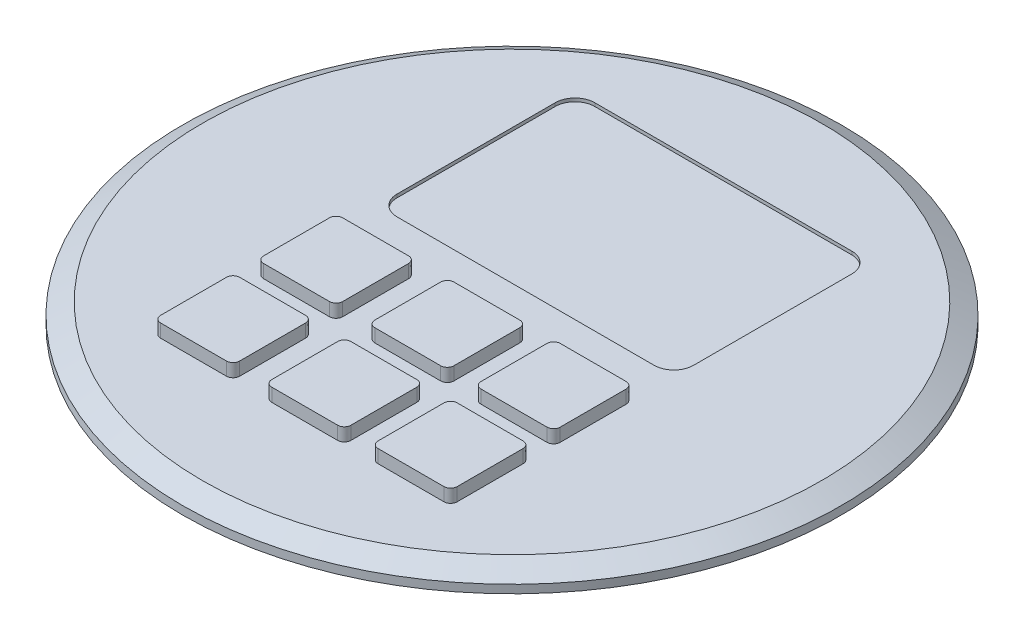
SolidWorks part; units mm, degrees
ref_plane "Front Plane" through (0, 0, 0) normal (0, 0, 1) x (1, 0, 0)
ref_plane "Top Plane" through (0, 0, 0) normal (0, 1, 0) x (1, 0, 0)
ref_plane "Right Plane" through (0, 0, 0) normal (1, 0, 0) x (0, 0, -1)
sketch "Sketch1" plane through (0, 0, 0) normal (0, 1, 0) x (1, 0, 0)
  circle A0 centre (0, 0) radius 50
extrude "Boss-Extrude1" add sketch "Sketch1" along normal blind 3
chamfer "Chamfer1" distance 1.75 angle 60 1 edges at (0, 3, 50)
sketch "Sketch2" plane through (0, 3, 0) normal (0, 1, 0) x (1, 0, 0)
  line L0 (11.1037, -15.7945) -> (21.1037, -15.7945)
  line L1 (-19.8963, 30) -> (19.1037, 30)
  line L2 (-22.8963, 27) -> (-22.8963, 3)
  line L3 (-19.8963, 0) -> (19.1037, 0)
  line L4 (22.1037, 27) -> (22.1037, 3)
  line L5 (-22.8963, 30) -> (22.1037, 0) construction
  line L6 (-22.8963, 0) -> (22.1037, 30) construction
  line L7 (-21.8963, -3.7945) -> (-11.8963, -3.7945)
  line L8 (-22.8963, -4.7945) -> (-22.8963, -14.7945)
  line L9 (-21.8963, -15.7945) -> (-11.8963, -15.7945)
  line L10 (-10.8963, -4.7945) -> (-10.8963, -14.7945)
  line L11 (-22.8963, -3.7945) -> (-10.8963, -15.7945) construction
  line L12 (-22.8963, -15.7945) -> (-10.8963, -3.7945) construction
  line L13 (10.1037, -4.7945) -> (10.1037, -14.7945)
  line L14 (22.1037, -4.7945) -> (22.1037, -14.7945)
  line L15 (11.1037, -3.7945) -> (21.1037, -3.7945)
  line L16 (-6.0233, -4.7945) -> (-6.0233, -14.7945)
  line L17 (-5.0233, -3.7945) -> (4.9767, -3.7945)
  line L18 (5.9767, -4.7945) -> (5.9767, -14.7945)
  line L19 (-5.0233, -15.7945) -> (4.9767, -15.7945)
  line L20 (-26.8535, -17.6087) -> (27.7548, -17.6087) construction
  line L21 (22.1037, -30.4229) -> (22.1037, -20.4229)
  line L22 (11.1037, -19.4229) -> (21.1037, -19.4229)
  line L23 (10.1037, -30.4229) -> (10.1037, -20.4229)
  line L24 (11.1037, -31.4229) -> (21.1037, -31.4229)
  line L25 (-5.0233, -31.4229) -> (4.9767, -31.4229)
  line L26 (5.9767, -30.4229) -> (5.9767, -20.4229)
  line L27 (-5.0233, -19.4229) -> (4.9767, -19.4229)
  line L28 (-6.0233, -30.4229) -> (-6.0233, -20.4229)
  line L29 (-21.8963, -19.4229) -> (-11.8963, -19.4229)
  line L30 (-10.8963, -30.4229) -> (-10.8963, -20.4229)
  line L31 (-21.8963, -31.4229) -> (-11.8963, -31.4229)
  line L32 (-22.8963, -30.4229) -> (-22.8963, -20.4229)
  line L33 (-19.8963, 0) -> (19.1037, 0)
  line L34 (-19.8963, 30) -> (19.1037, 30)
  line L35 (-22.8963, 27) -> (-22.8963, 3)
  line L36 (22.1037, 27) -> (22.1037, 3)
  arc A0 (22.1037, 27) -> (19.1037, 30) centre (19.1037, 27) ccw
  arc A1 (19.1037, 0) -> (22.1037, 3) centre (19.1037, 3) ccw
  arc A2 (-22.8963, 3) -> (-19.8963, 0) centre (-19.8963, 3) ccw
  arc A3 (-22.8963, 27) -> (-19.8963, 30) centre (-19.8963, 27) cw
  arc A4 (-10.8963, -4.7945) -> (-11.8963, -3.7945) centre (-11.8963, -4.7945) ccw
  arc A5 (-21.8963, -15.7945) -> (-22.8963, -14.7945) centre (-21.8963, -14.7945) cw
  arc A6 (-10.8963, -14.7945) -> (-11.8963, -15.7945) centre (-11.8963, -14.7945) cw
  arc A7 (-22.8963, -4.7945) -> (-21.8963, -3.7945) centre (-21.8963, -4.7945) cw
  arc A8 (22.1037, -4.7945) -> (21.1037, -3.7945) centre (21.1037, -4.7945) ccw
  arc A9 (10.1037, -4.7945) -> (11.1037, -3.7945) centre (11.1037, -4.7945) cw
  arc A10 (11.1037, -15.7945) -> (10.1037, -14.7945) centre (11.1037, -14.7945) cw
  arc A11 (22.1037, -14.7945) -> (21.1037, -15.7945) centre (21.1037, -14.7945) cw
  arc A12 (5.9767, -4.7945) -> (4.9767, -3.7945) centre (4.9767, -4.7945) ccw
  arc A13 (5.9767, -14.7945) -> (4.9767, -15.7945) centre (4.9767, -14.7945) cw
  arc A14 (-5.0233, -15.7945) -> (-6.0233, -14.7945) centre (-5.0233, -14.7945) cw
  arc A15 (-6.0233, -4.7945) -> (-5.0233, -3.7945) centre (-5.0233, -4.7945) cw
  arc A16 (22.1037, -20.4229) -> (21.1037, -19.4229) centre (21.1037, -20.4229) ccw
  arc A17 (11.1037, -19.4229) -> (10.1037, -20.4229) centre (11.1037, -20.4229) ccw
  arc A18 (10.1037, -30.4229) -> (11.1037, -31.4229) centre (11.1037, -30.4229) ccw
  arc A19 (22.1037, -30.4229) -> (21.1037, -31.4229) centre (21.1037, -30.4229) cw
  arc A20 (-6.0233, -30.4229) -> (-5.0233, -31.4229) centre (-5.0233, -30.4229) ccw
  arc A21 (5.9767, -30.4229) -> (4.9767, -31.4229) centre (4.9767, -30.4229) cw
  arc A22 (5.9767, -20.4229) -> (4.9767, -19.4229) centre (4.9767, -20.4229) ccw
  arc A23 (-5.0233, -19.4229) -> (-6.0233, -20.4229) centre (-5.0233, -20.4229) ccw
  arc A24 (-10.8963, -20.4229) -> (-11.8963, -19.4229) centre (-11.8963, -20.4229) ccw
  arc A25 (-10.8963, -30.4229) -> (-11.8963, -31.4229) centre (-11.8963, -30.4229) cw
  arc A26 (-21.8963, -19.4229) -> (-22.8963, -20.4229) centre (-21.8963, -20.4229) ccw
  arc A27 (-22.8963, -30.4229) -> (-21.8963, -31.4229) centre (-21.8963, -30.4229) ccw
  arc A28 (19.1037, 0) -> (22.1037, 3) centre (19.1037, 3) ccw
  arc A29 (-22.8963, 27) -> (-19.8963, 30) centre (-19.8963, 27) cw
  arc A30 (22.1037, 27) -> (19.1037, 30) centre (19.1037, 27) ccw
  arc A31 (-22.8963, 3) -> (-19.8963, 0) centre (-19.8963, 3) ccw
  point P0 (-0.3963, 15)
  point P17 (-16.8963, -9.7945)
  dimension "D3" = 3
  dimension "D6" = 1
  dimension "D1" = 30
  dimension "D2" = 45
  dimension "D4" = 12
  dimension "D5" = 12
  dimension "D7" = 4.1271
extrude "Boss-Extrude2" add sketch "Sketch2" along normal blind 2 contours A8 L15 A9 L13 A10 L0 A11 L14 | L16 A14 L19 A13 L18 A12 L17 A15 | L7 A4 L10 A6 L9 A5 L8 A7 | L29 A24 L30 A25 L31 A27 L32 A26 | A20 L25 A21 L26 A22 L27 A23 L28 | L21 A16 L22 A17 L23 A18 L24 A19
sketch "Sketch3" plane through (0, 3, 0) normal (0, 1, 0) x (1, 0, 0)
  line L0 (-19.8963, 32.4539) -> (19.1037, 32.4539)
  line L1 (-22.8963, 29.4539) -> (-22.8963, 5.4539)
  line L2 (-19.8963, 2.4539) -> (19.1037, 2.4539)
  line L3 (22.1037, 29.4539) -> (22.1037, 5.4539)
  line L4 (-22.8963, -4.7945) -> (-22.8963, -14.7945) construction
  arc A0 (22.1037, 29.4539) -> (19.1037, 32.4539) centre (19.1037, 29.4539) ccw
  arc A1 (19.1037, 2.4539) -> (22.1037, 5.4539) centre (19.1037, 5.4539) ccw
  arc A2 (-22.8963, 5.4539) -> (-19.8963, 2.4539) centre (-19.8963, 5.4539) ccw
  arc A3 (-22.8963, 29.4539) -> (-19.8963, 32.4539) centre (-19.8963, 29.4539) cw
extrude "Cut-Extrude1" cut sketch "Sketch3" against normal blind 0.5 contours L0 A0 L3 A1 L2 A2 L1 A3
